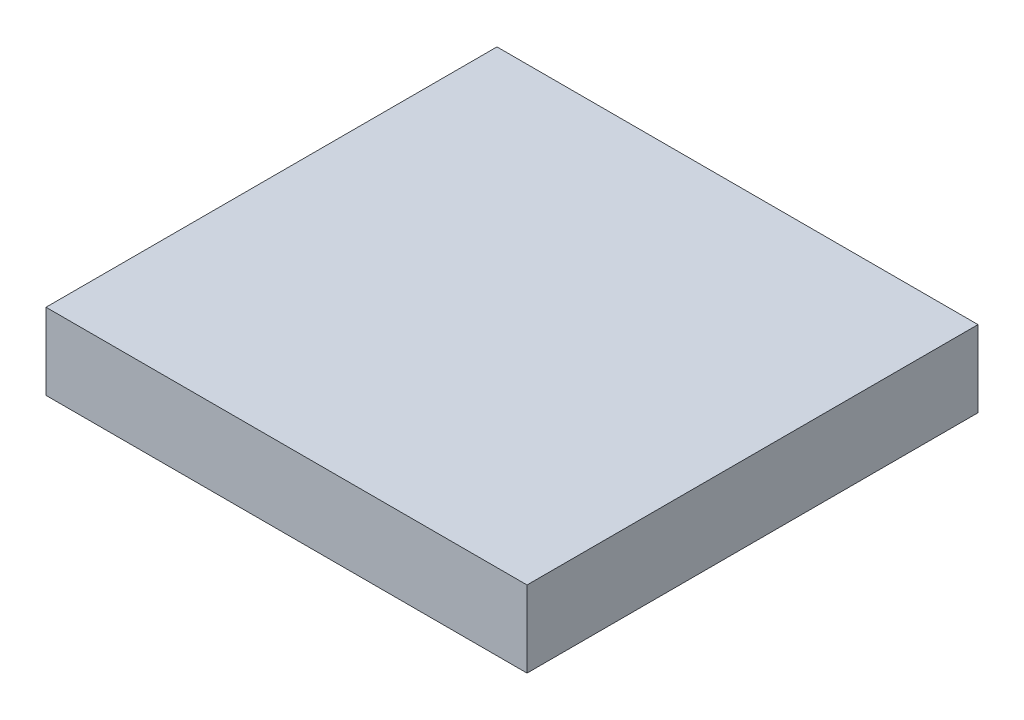
SolidWorks part; units mm, degrees
ref_plane "Front Plane" through (0, 0, 0) normal (0, 0, 1) x (1, 0, 0)
ref_plane "Top Plane" through (0, 0, 0) normal (0, 1, 0) x (1, 0, 0)
ref_plane "Right Plane" through (0, 0, 0) normal (1, 0, 0) x (0, 0, -1)
sketch "Sketch1" plane through (0, 0, 0) normal (0, 1, 0) x (1, 0, 0)
  line L1 (0, 0) -> (96, 0)
  line L2 (0, 0) -> (0, 90)
  line L3 (0, 90) -> (96, 90)
  line L4 (96, 0) -> (96, 90)
  dimension "D1" = 96
  dimension "D2" = 90
extrude "Boss-Extrude1" add sketch "Sketch1" along normal blind 15.24
